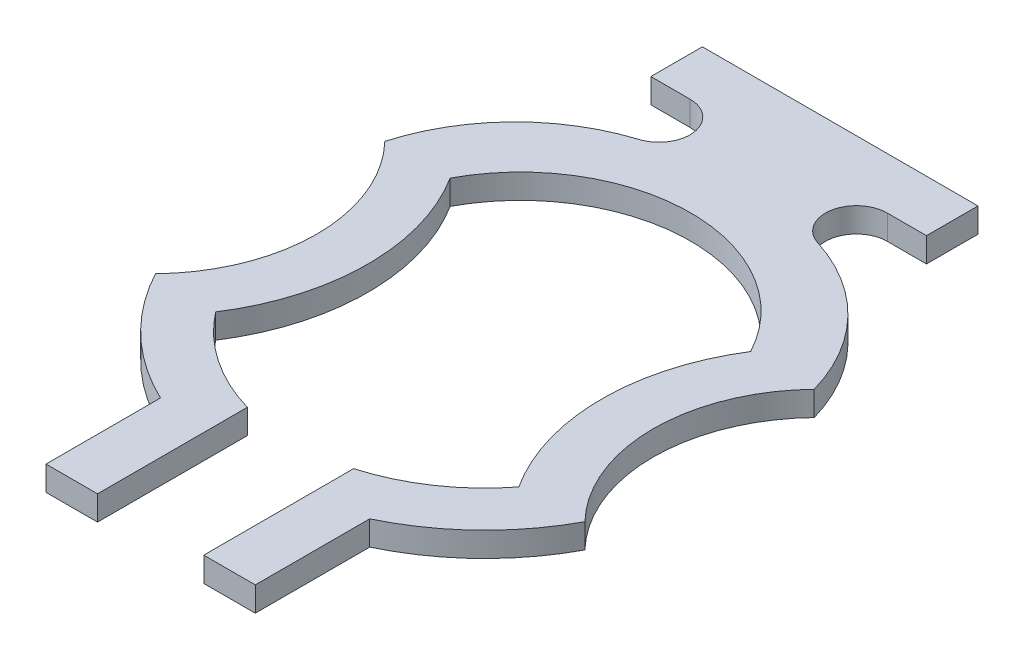
SolidWorks part; units mm, degrees
ref_plane "Alzado" through (0, 0, 0) normal (0, 0, 1) x (1, 0, 0)
ref_plane "Planta" through (0, 0, 0) normal (0, 1, 0) x (1, 0, 0)
ref_plane "Vista lateral" through (0, 0, 0) normal (1, 0, 0) x (0, 0, -1)
sketch "Sketch1" plane through (0, 0, 0) normal (0, 1, 0) x (1, 0, 0)
  line L0 (0.2165, -1000.9575) -> (0.2165, 48999.0425) construction
  line L1 (0.4265, -1000.9802) -> (0.4265, 48999.0198) construction
  line L2 (0.5617, -1001.0075) -> (0.5617, 48998.9925) construction
  line L3 (-999.2046, 1.4483) -> (49000.7954, 1.4483) construction
  line L4 (-999.3251, 1.2383) -> (49000.6749, 1.2383) construction
  line L5 (-0.5617, 1.4483) -> (0.5617, 1.4483)
  line L6 (0.5617, 1.4483) -> (0.5617, 1.2383)
  line L7 (-999.188, -1.3623) -> (49000.812, -1.3623) construction
  line L8 (-0.2165, -0.7515) -> (-0.2165, -1.3623)
  line L9 (-0.2165, -1.3623) -> (-0.4265, -1.3623)
  line L10 (-0.4265, -1.3623) -> (-0.4265, -0.8957)
  line L11 (0, -1000) -> (0, 49000) construction
  line L12 (-1000, 0) -> (49000, 0) construction
  line L13 (1.3587, -1000.0419) -> (1.3587, 48999.9581) construction
  line L14 (-1000, 0.1447) -> (49000, 0.1447) construction
  line L15 (0.2165, -0.7515) -> (0.2165, -1.3623)
  line L16 (0.2165, -1.3623) -> (0.4265, -1.3623)
  line L17 (0.4265, -1.3623) -> (0.4265, -0.8957)
  line L18 (-1000.0995, 0.2553) -> (48999.9005, 0.2553) construction
  line L19 (0.1326, -999.6898) -> (0.1326, 49000.3102) construction
  line L20 (0.4022, 1.2383) -> (0.5617, 1.2383)
  line L21 (-0.4022, 1.2383) -> (-0.5617, 1.2383)
  line L22 (-0.5617, 1.4483) -> (-0.5617, 1.2383)
  arc A0 (-0.6123, 0.4709) -> (-0.6178, -0.4795) centre (-1.3587, 0) cw
  arc A1 (-0.2165, -0.7515) -> (-0.6178, -0.4795) centre (0, 0) cw
  arc A2 (0.8751, 0.4673) -> (0.8751, -0.4673) centre (1.3587, 0) ccw
  arc A3 (0.4022, 1.2383) -> (0.3643, 0.9919) centre (0.4022, 1.1122) ccw
  arc A4 (0.6123, 0.4709) -> (-0.6123, 0.4709) centre (0, 0.1447) ccw
  arc A5 (0.2165, -0.7515) -> (0.6178, -0.4795) centre (0, 0) ccw
  arc A6 (0.4265, -0.8957) -> (0.8751, -0.4673) centre (0, 0) ccw
  arc A7 (0.8751, 0.4673) -> (0.3643, 0.9919) centre (0.1326, 0.2553) ccw
  arc A8 (-0.4265, -0.8957) -> (-0.8751, -0.4673) centre (0, 0) cw
  arc A9 (-0.8751, 0.4673) -> (-0.8751, -0.4673) centre (-1.3587, 0) cw
  arc A10 (-0.8751, 0.4673) -> (-0.3643, 0.9919) centre (-0.1326, 0.2553) cw
  arc A11 (-0.4022, 1.2383) -> (-0.3643, 0.9919) centre (-0.4022, 1.1122) cw
  arc A13 (0.6123, 0.4709) -> (0.6178, -0.4795) centre (1.3587, 0) ccw
  point P21 (1.3587, 0)
  point P55 (0.1326, 0.2553)
  point P59 (0, 1.4483)
  dimension "D3" = 0.7821
  dimension "D4" = 0.9921
  dimension "D5" = 0.2165
  dimension "D6" = 0.4265
  dimension "D7" = 0.6725
  dimension "D8" = 0.5617
  dimension "D9" = 1.3623
  dimension "D10" = 1.4483
  dimension "D11" = 0.1261
  dimension "D12" = 1.2383
  dimension "D13" = 1.3587
  dimension "D15" = 0.7722
  dimension "D18" = 0.6938
  dimension "D25" = 0.8825
  dimension "D17" = 0.1447
  dimension "D21" = 0.2553
  dimension "D23" = 0.1326
extrude "Boss-Extrude1" add sketch "Sketch1" along normal blind 0.1
